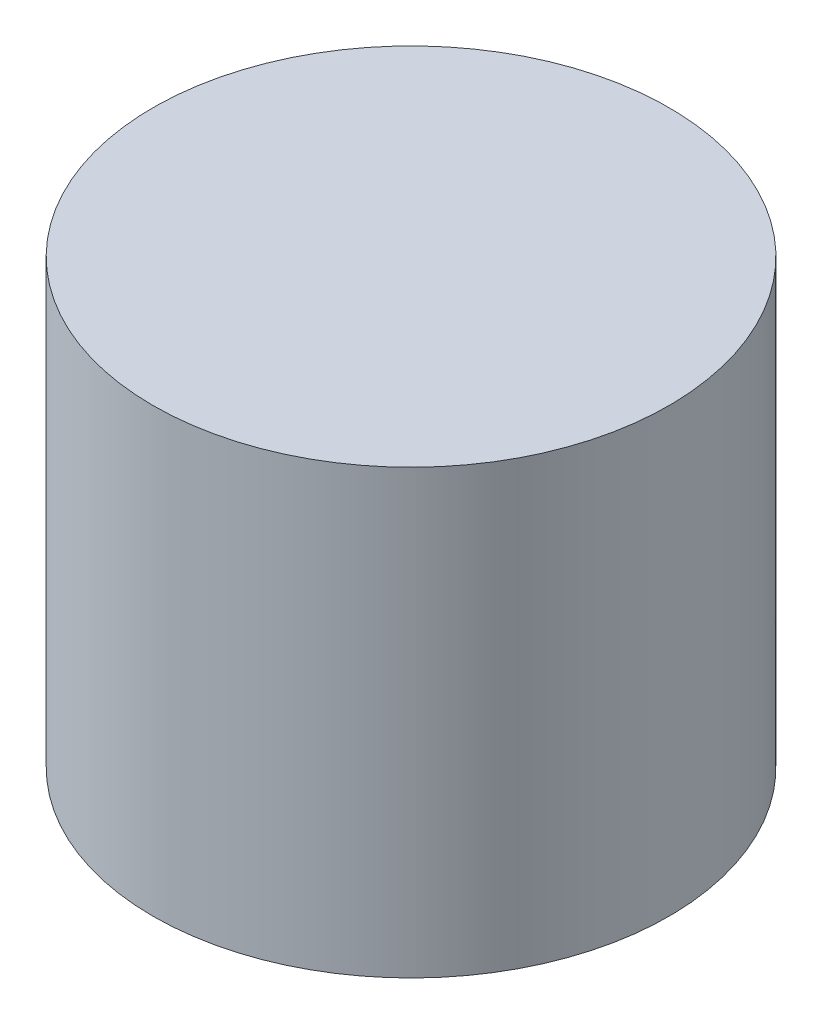
SolidWorks part; units mm, degrees
ref_plane "Front Plane" through (0, 0, 0) normal (0, 0, 1) x (1, 0, 0)
ref_plane "Top Plane" through (0, 0, 0) normal (0, 1, 0) x (1, 0, 0)
ref_plane "Right Plane" through (0, 0, 0) normal (1, 0, 0) x (0, 0, -1)
sketch "Sketch1" plane through (0, 0, 0) normal (0, 1, 0) x (1, 0, 0)
  circle A0 centre (0, -3.0091) radius 3.15
extrude "Boss-Extrude1" add sketch "Sketch1" along normal blind 5.4
